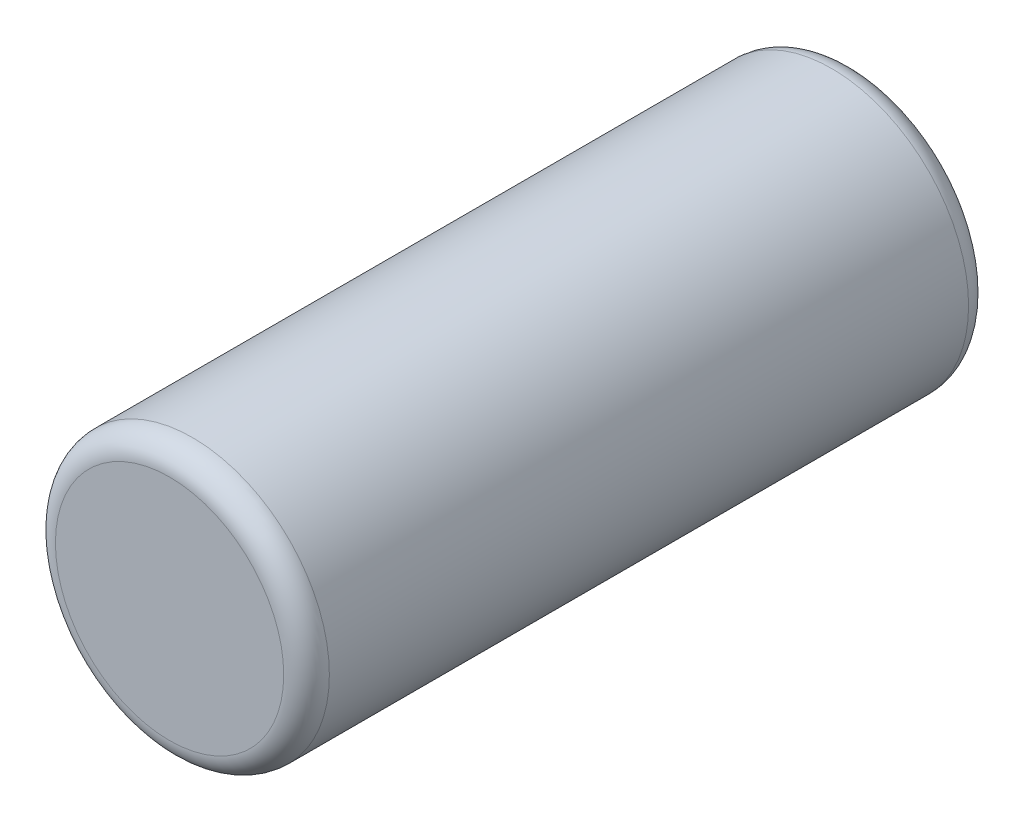
SolidWorks part; units mm, degrees
ref_plane "Plan de face" through (0, 0, 0) normal (0, 0, 1) x (1, 0, 0)
ref_plane "Plan de dessus" through (0, 0, 0) normal (0, 1, 0) x (1, 0, 0)
ref_plane "Plan de droite" through (0, 0, 0) normal (1, 0, 0) x (0, 0, -1)
sketch "Esquisse1" plane through (0, 0, 0) normal (0, 0, 1) x (1, 0, 0)
  circle A0 centre (0, 0) radius 6
extrude "Boss.-Extru.1" add sketch "Esquisse1" along normal blind 30
fillet "Congé1" radius 1 2 edges at (6, 0, 0) (6, 0, 30)
